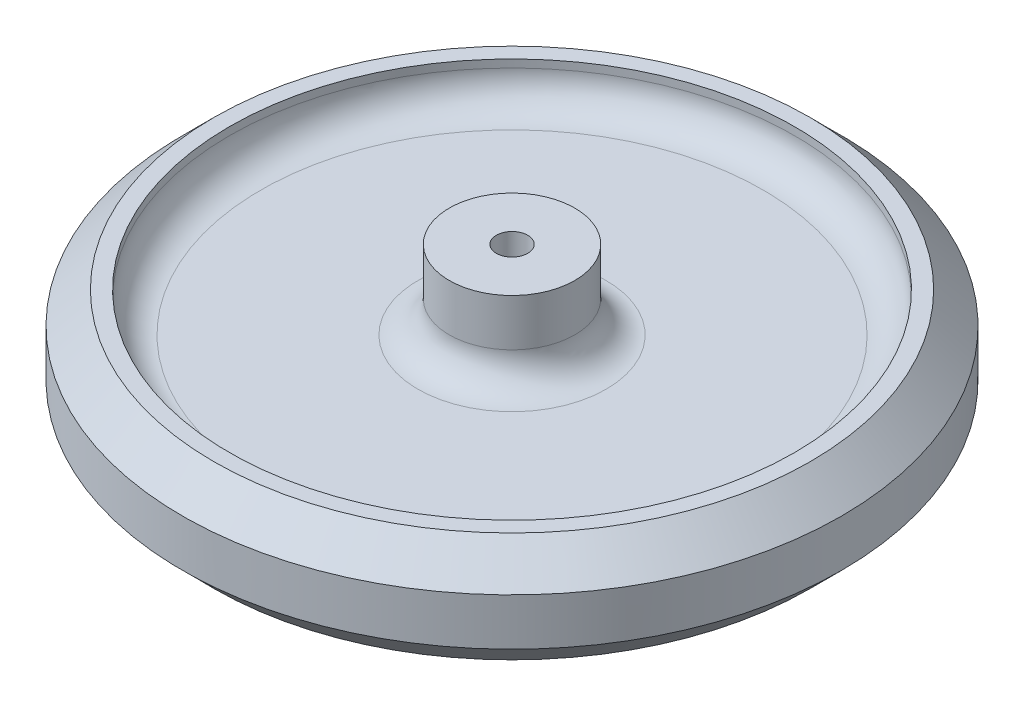
SolidWorks part; units mm, degrees
material "Brass"
ref_plane "Front Plane" through (0, 0, 0) normal (0, 0, 1) x (1, 0, 0)
ref_plane "Top Plane" through (0, 0, 0) normal (0, 1, 0) x (1, 0, 0)
ref_plane "Right Plane" through (0, 0, 0) normal (1, 0, 0) x (0, 0, -1)
sketch "Sketch1" plane through (0, 0, 0) normal (0, 0, 1) x (1, 0, 0)
  line L0 (0, -9.525) -> (0, 9.525) construction
  line L1 (-6.35, 9.525) -> (-1.5875, 9.525)
  line L2 (-6.35, 9.525) -> (-6.35, 1.5875)
  line L3 (-6.35, 1.5875) -> (-28.575, 1.5875)
  line L4 (-28.575, 1.5875) -> (-28.575, 5.5562)
  line L5 (-28.575, 5.5562) -> (-33.3375, 5.5562)
  line L6 (-33.3375, 5.5562) -> (-33.3375, -5.5563)
  line L7 (-33.3375, -5.5563) -> (-28.575, -5.5563)
  line L8 (-28.575, -5.5563) -> (-28.575, -1.5875)
  line L9 (-28.575, -1.5875) -> (-6.35, -1.5875)
  line L10 (-6.35, -1.5875) -> (-6.35, -9.525)
  line L11 (-1.5875, 9.525) -> (-1.5875, -9.525)
  line L12 (-1.5875, -9.525) -> (-6.35, -9.525)
  point P4 (0, 0)
  dimension "D1" = 66.675
  dimension "D2" = 3.175
  dimension "D3" = 19.05
  dimension "D4" = 4.7625
  dimension "D5" = 12.7
  dimension "D6" = 11.1125
  dimension "D7" = 3.175
revolve "Revolve1" add sketch "Sketch1" angle 360 about L0
fillet "Fillet1" radius 3.175 4 edges at (28.575, -1.5875, 0) (6.35, -1.5875, 0) (6.35, 1.5875, 0) (28.575, 1.5875, 0)
chamfer "Chamfer1" distance 3.175 angle 45 2 edges at (33.3375, 5.5563, 0) (33.3375, -5.5562, 0)
